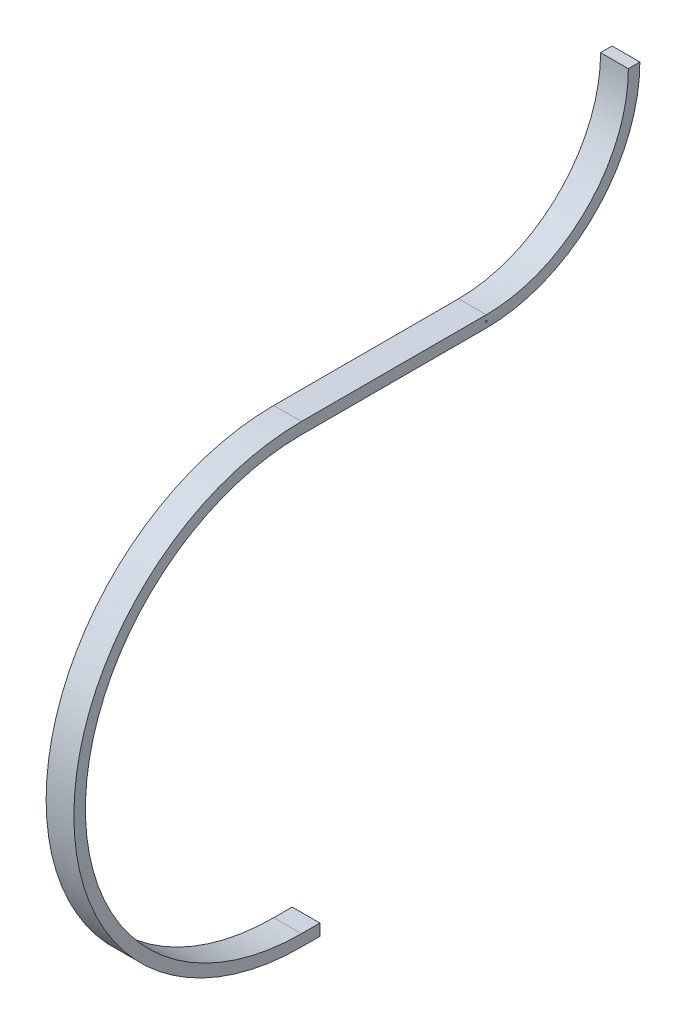
SolidWorks part; units mm, degrees
ref_plane "Front Plane" through (0, 0, 0) normal (0, 0, 1) x (1, 0, 0)
ref_plane "Top Plane" through (0, 0, 0) normal (0, 1, 0) x (1, 0, 0)
ref_plane "Right Plane" through (0, 0, 0) normal (1, 0, 0) x (0, 0, -1)
sketch "Sketch1" plane through (0, 0, 0) normal (0, 0, 1) x (1, 0, 0)
  line L1 (-9.525, 3.9624) -> (9.525, 3.9624)
  line L2 (-9.525, 3.9624) -> (-9.525, -3.9624)
  line L3 (-9.525, -3.9624) -> (9.525, -3.9624)
  line L4 (9.525, 3.9624) -> (9.525, -3.9624)
  line L5 (-9.525, 3.9624) -> (9.525, -3.9624) construction
  line L6 (-9.525, -3.9624) -> (9.525, 3.9624) construction
  point P0 (0, 0)
  dimension "D1" = 19.05
  dimension "D2" = 7.9248
sketch "Sketch2" plane through (0, 0, 0) normal (1, 0, 0) x (0, 0, -1)
  line L0 (0, 0) -> (0, 304.8) construction
  line L1 (0, 304.8) -> (127, 304.8)
  arc A0 (0, 304.8) -> (0, 0) centre (0, 152.4) ccw
  arc A1 (127, 304.8) -> (228.6, 406.4) centre (127, 406.4) ccw
  dimension "D1" = 304.8
  dimension "D2" = 127
  dimension "D3" = 101.6
sweep "Sweep1" add profiles "Sketch1" path "Sketch2"
sketch "Sketch3" plane through (9.525, 0, 0) normal (1, 0, 0) x (0, 0, -1)
  line L0 (0, -3.9624) -> (0, 3.9624) construction
  line L1 (0, -3.9624) -> (0, 3.9624)
  line L2 (0, 3.9624) -> (12.7, 3.9624)
  line L3 (12.7, 3.9624) -> (12.7, -3.9624)
  line L4 (12.7, -3.9624) -> (0, -3.9624)
  dimension "D1" = 12.7
extrude "Boss-Extrude1" add sketch "Sketch3" against normal up to surface (19.05 mm away) up to face at (-9.525, 248.7395, -56.0605)
hole_wizard "#56 (0.0465) Diameter Hole1" positions "Sketch5" profile "Sketch6" hole size "#56" standard "Ansi Inch" end condition through all
sketch "Sketch5" plane through (9.525, 0, 0) normal (1, 0, 0) x (0, 0, -1)
  line L0 (127, 308.7624) -> (127, 300.8376) construction
  point P0 (127, 304.8)
sketch "Sketch6" plane through (9.525, 304.8, -127) normal (0, 1, 0) x (0, 0, -1)
  line L0 (0, 0) -> (0, 19.05)
  line L1 (0, 19.05) -> (0.5905, 19.05)
  line L2 (0.5905, 19.05) -> (0.5905, 0)
  line L5 (0.5905, 0) -> (0, 0)
  line L11 (0, -6.35) -> (0, 107.95) construction
  dimension "Thru Hole Dia." = 1.1811
  dimension "Thru Hole Depth" = 19.05
